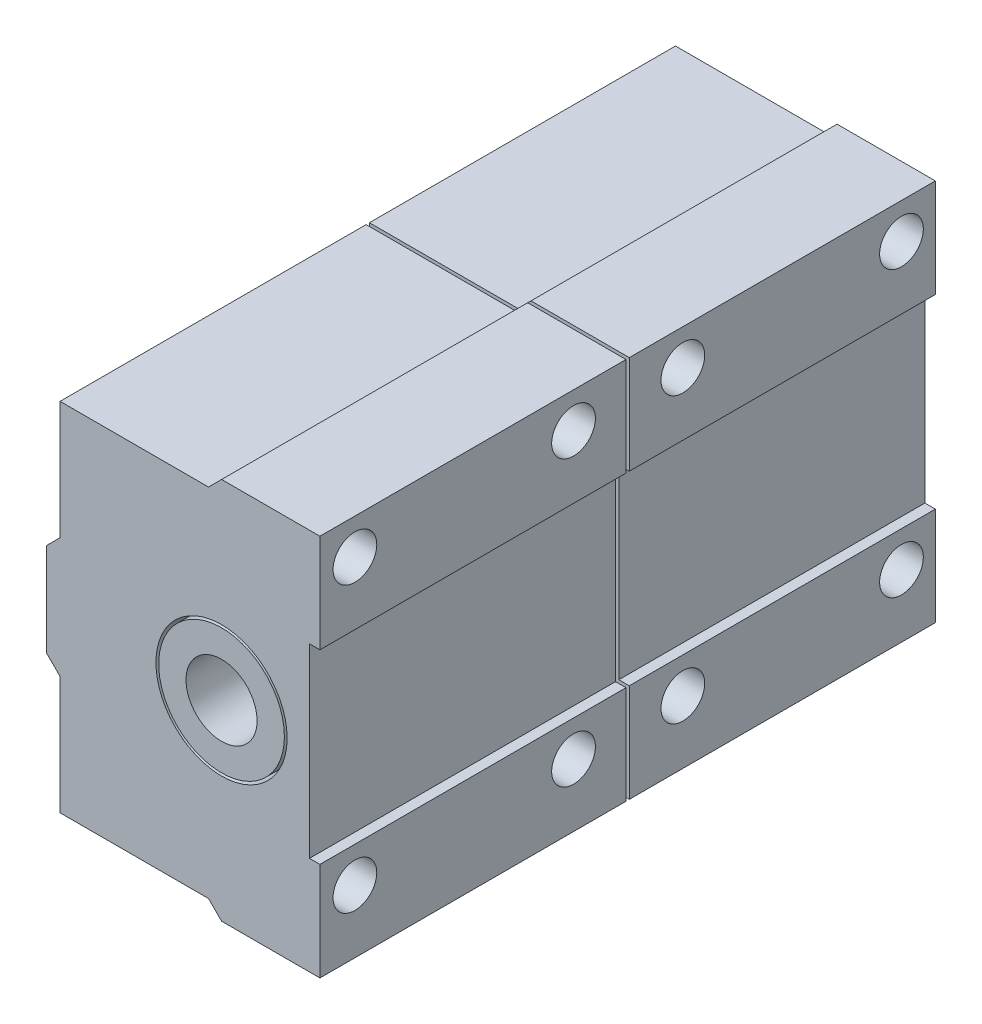
SolidWorks part; units mm, degrees
ref_plane "Front Plane" through (0, 0, 0) normal (0, 0, 1) x (1, 0, 0)
ref_plane "Top Plane" through (0, 0, 0) normal (0, 1, 0) x (1, 0, 0)
ref_plane "Right Plane" through (0, 0, 0) normal (1, 0, 0) x (0, 0, -1)
sketch "Sketch1" plane through (76.9692, 0, 0) normal (-1, 0, 0) x (0, 0, 1)
  line L0 (225, 26.8) -> (3, 26.8) construction
  line L1 (198.2, 25.05) -> (226.2, 25.05)
  line L2 (198.2, 25.05) -> (198.2, -9.95)
  line L3 (198.2, -9.95) -> (226.2, -9.95)
  line L4 (226.2, 25.05) -> (226.2, -9.95)
  line L5 (197.9, 25.05) -> (169.9, 25.05)
  line L6 (197.9, 25.05) -> (197.9, -9.95)
  line L7 (197.9, -9.95) -> (169.9, -9.95)
  line L8 (169.9, 25.05) -> (169.9, -9.95)
  line L10 (228, 23.8) -> (228, -18.2) construction
  dimension "D1" = 0.3
  dimension "D2" = 28
  dimension "D3" = 28
  dimension "D4" = 35
  dimension "D5" = 35
  dimension "D6" = 1.75
  dimension "D7" = 1.75
  dimension "D8" = 1.8
extrude "Boss-Extrude1" add sketch "Sketch1" along normal blind 25
sketch "Sketch4" plane through (76.9692, 0, 0) normal (1, 0, 0) x (0, 0, -1)
  circle A0 centre (-193, 21.8) radius 2
  circle A1 centre (-173, 21.8) radius 2
  circle A2 centre (-173, -4.2) radius 2
  circle A3 centre (-193, -4.2) radius 2
  circle A4 centre (-223, -4.2) radius 2
  circle A5 centre (-203, -4.2) radius 2
  circle A6 centre (-203, 21.8) radius 2
  circle A7 centre (-223, 21.8) radius 2
  dimension "D1" = 4
extrude "Cut-Extrude1" cut sketch "Sketch4" against normal blind 10
sketch "Sketch5" plane through (51.9692, 0, 0) normal (-1, 0, 0) x (0, 0, 1)
  circle A0 centre (223, 21.8) radius 1
  circle A1 centre (223, -4.2) radius 1
  circle A2 centre (203, -4.2) radius 1
  circle A3 centre (203, 21.8) radius 1
  circle A4 centre (193, 21.8) radius 1
  circle A5 centre (193, -4.2) radius 1
  circle A6 centre (173, -4.2) radius 1
  circle A7 centre (173, 21.8) radius 1
  dimension "D1" = 2
extrude "Cut-Extrude2" cut sketch "Sketch5" against normal blind 3
sketch "Sketch6" plane through (0, 0, 226.2) normal (0, 0, 1) x (1, 0, 0)
  line L0 (76.9692, 23.8) -> (76.9692, -18.2) construction
  circle A0 centre (67.9692, 7.55) radius 6
  dimension "D3" = 12
  dimension "D1" = 9
extrude "Cut-Extrude3" cut sketch "Sketch6" against normal blind 82
sketch "Sketch7" plane through (0, 0, 226.2) normal (0, 0, 1) x (1, 0, 0)
  line L0 (76.9692, 23.8) -> (76.9692, -18.2) construction
  line L1 (76.9692, -0.95) -> (76.012, -0.95)
  line L2 (76.9692, -0.95) -> (76.9692, 16.05)
  line L3 (76.9692, 16.05) -> (76.012, 16.05)
  line L4 (76.012, -0.95) -> (76.012, 16.05)
  line L5 (51.9692, 25.05) -> (76.9692, 25.05) construction
  line L6 (51.9692, -9.95) -> (76.9692, -9.95) construction
  dimension "D1" = 9
  dimension "D2" = 9
extrude "Cut-Extrude4" cut sketch "Sketch7" against normal blind 82
sketch "Sketch8" plane through (0, 0, 226.2) normal (0, 0, 1) x (1, 0, 0)
  line L0 (67.9764, 25.05) -> (66.7764, 23.85)
  line L1 (51.9692, 25.05) -> (76.9692, 25.05) construction
  line L2 (66.7764, 23.85) -> (53.1958, 23.85)
  line L3 (65.5596, 13.0449) -> (50.3648, 13.0449) construction
  line L4 (65.5596, 2.0551) -> (50.3648, 2.0551) construction
  line L5 (53.1958, 23.85) -> (53.1958, 13.0449)
  line L6 (53.1958, 13.0449) -> (51.9692, 11.8183)
  line L7 (51.9692, -9.95) -> (51.9692, 25.05) construction
  line L8 (53.1958, 2.0551) -> (51.9692, 3.2817)
  line L9 (53.1958, 2.0551) -> (53.1958, -8.75)
  line L10 (53.1958, -8.75) -> (66.7764, -8.75)
  line L11 (66.7764, -8.75) -> (67.9764, -9.95)
  line L12 (51.9692, -9.95) -> (76.9692, -9.95) construction
  line L14 (51.9692, 25.05) -> (67.9764, 25.05)
  line L15 (51.9692, -9.95) -> (67.9764, -9.95)
  line L16 (51.9692, -9.95) -> (51.9692, 3.2817)
  line L17 (51.9692, 11.8183) -> (51.9692, 25.05)
  circle A0 centre (67.9692, 7.55) radius 6 construction
  dimension "D1" = 1.2
  dimension "D2" = 1.2
  dimension "D3" = 45
  dimension "D4" = 45
  dimension "D5" = 45
extrude "Cut-Extrude5" cut sketch "Sketch8" against normal blind 82
sketch "Sketch9" plane through (0, 0, 226.2) normal (0, 0, 1) x (1, 0, 0)
  circle A0 centre (67.9692, 7.55) radius 5.75
  circle A1 centre (67.9692, 7.55) radius 3.25
  dimension "D1" = 6.5
  dimension "D2" = 11.5
extrude "Boss-Extrude2" add sketch "Sketch9" against normal up to surface (56.3 mm away) up to face at (73.9692, 7.55, 169.9)
